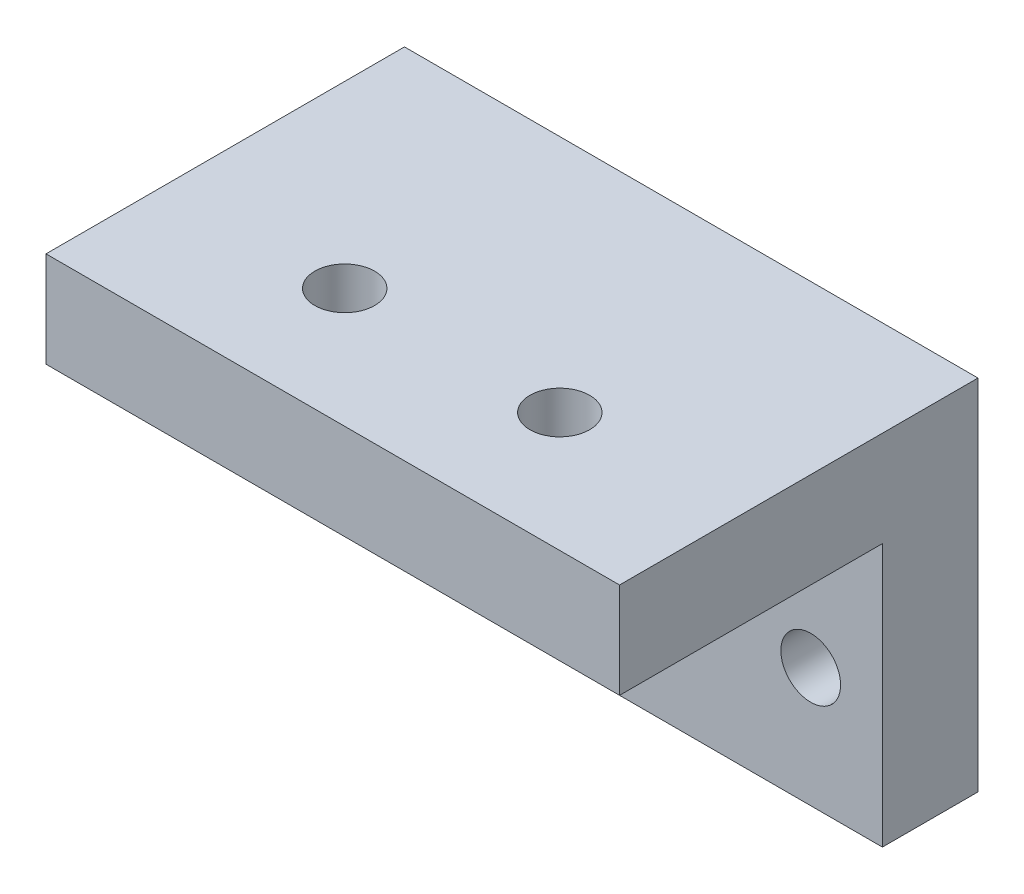
SolidWorks part; units mm, degrees
material "1060 合金"
ref_plane "前视基准面" through (0, 0, 0) normal (0, 0, 1) x (1, 0, 0)
ref_plane "上视基准面" through (0, 0, 0) normal (0, 1, 0) x (1, 0, 0)
ref_plane "右视基准面" through (0, 0, 0) normal (1, 0, 0) x (0, 0, -1)
other "Configuration Table"
sketch "草图1" plane through (0, 0, 0) normal (0, 0, 1) x (1, 0, 0)
  line L1 (-12, 7.5) -> (12, 7.5)
  line L2 (-12, 7.5) -> (-12, -7.5)
  line L3 (-12, -7.5) -> (12, -7.5)
  line L4 (12, 7.5) -> (12, -7.5)
  line L5 (-12, 7.5) -> (12, -7.5) construction
  line L6 (-12, -7.5) -> (12, 7.5) construction
  point P0 (0, 0)
  dimension "D1" = 24
  dimension "D2" = 15
extrude "凸台-拉伸1" add sketch "草图1" along normal blind 4
sketch "草图2" plane through (0, 0, 4) normal (0, 0, 1) x (1, 0, 0)
  line L0 (12, -7.5) -> (12, 7.5) construction
  line L1 (-12, 7.5) -> (12, 7.5)
  line L2 (-12, 7.5) -> (-12, 3.5)
  line L3 (-12, 3.5) -> (12, 3.5)
  line L4 (12, 7.5) -> (12, 3.5)
  dimension "D1" = 4
extrude "凸台-拉伸2" add sketch "草图2" along normal blind 11
sketch "草图3" plane through (0, 0, 4) normal (0, 0, 1) x (1, 0, 0)
  line L0 (0, 0) -> (0, -7.5) construction
  line L1 (-12, -7.5) -> (12, -7.5) construction
  line L2 (12, -7.5) -> (12, 3.5) construction
  circle A0 centre (-9, -2.5) radius 1.25
  circle A1 centre (9, -2.5) radius 1.25
  dimension "D2" = 2.5
  dimension "D1" = 3
  dimension "D3" = 5
extrude "切除-拉伸1" cut sketch "草图3" against normal through all
cosmetic thread "装饰螺纹线1" parameters "D2"=3
sketch "草图4" plane through (0, 3.5, 0) normal (0, -1, 0) x (1, 0, 0)
  line L0 (0, 15) -> (0, 4) construction
  line L1 (-12, 15) -> (12, 15) construction
  line L2 (-12, 4) -> (12, 4) construction
  line L3 (-12, 15) -> (-12, 4) construction
  circle A0 centre (-4.5, 10) radius 1.25
  circle A1 centre (4.5, 10) radius 1.25
  dimension "D1" = 2.5
  dimension "D2" = 5
  dimension "D3" = 7.5
extrude "切除-拉伸2" cut sketch "草图4" against normal through all
cosmetic thread "装饰螺纹线3" parameters "D2"=3
cosmetic thread "装饰螺纹线4" parameters "D2"=3
move or copy body "实体-移动/复制1" [suppressed] bodies to move or copy 109
